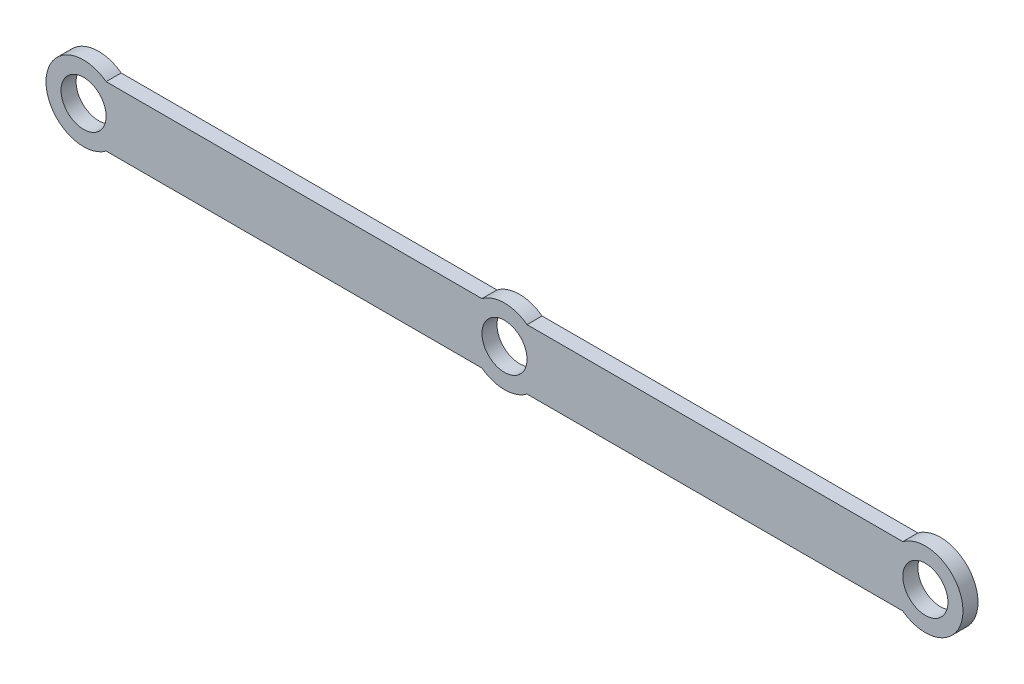
SolidWorks part; units mm, degrees
ref_plane "前视基准面" through (0, 0, 0) normal (0, 0, 1) x (1, 0, 0)
ref_plane "上视基准面" through (0, 0, 0) normal (0, 1, 0) x (1, 0, 0)
ref_plane "右视基准面" through (0, 0, 0) normal (1, 0, 0) x (0, 0, -1)
sketch "草图1" plane through (0, 0, 0) normal (0, 0, 1) x (1, 0, 0)
  line L0 (1.5, 2) -> (26.5, 2)
  line L1 (-26.5, 2) -> (-1.5, 2)
  line L2 (1.5, -2) -> (26.5, -2)
  line L3 (-26.5, -2) -> (-1.5, -2)
  arc A0 (26.5, -2) -> (26.5, 2) centre (28, 0) ccw
  arc A1 (-26.5, 2) -> (-26.5, -2) centre (-28, 0) ccw
  arc A2 (1.5, 2) -> (-1.5, 2) centre (0, 0) ccw
  circle A3 centre (-28, 0) radius 1.5
  circle A4 centre (0, 0) radius 1.5
  circle A5 centre (28, 0) radius 1.5
  arc A6 (-1.5, -2) -> (1.5, -2) centre (0, 0) ccw
  point P0 (0, 0)
  dimension "D1" = 5
  dimension "D3" = 5
  dimension "D5" = 5
  dimension "D2" = 4
  dimension "D4" = 2
  dimension "D6" = 28
  dimension "D7" = 28
extrude "凸台-拉伸1" add sketch "草图1" along normal blind 1
